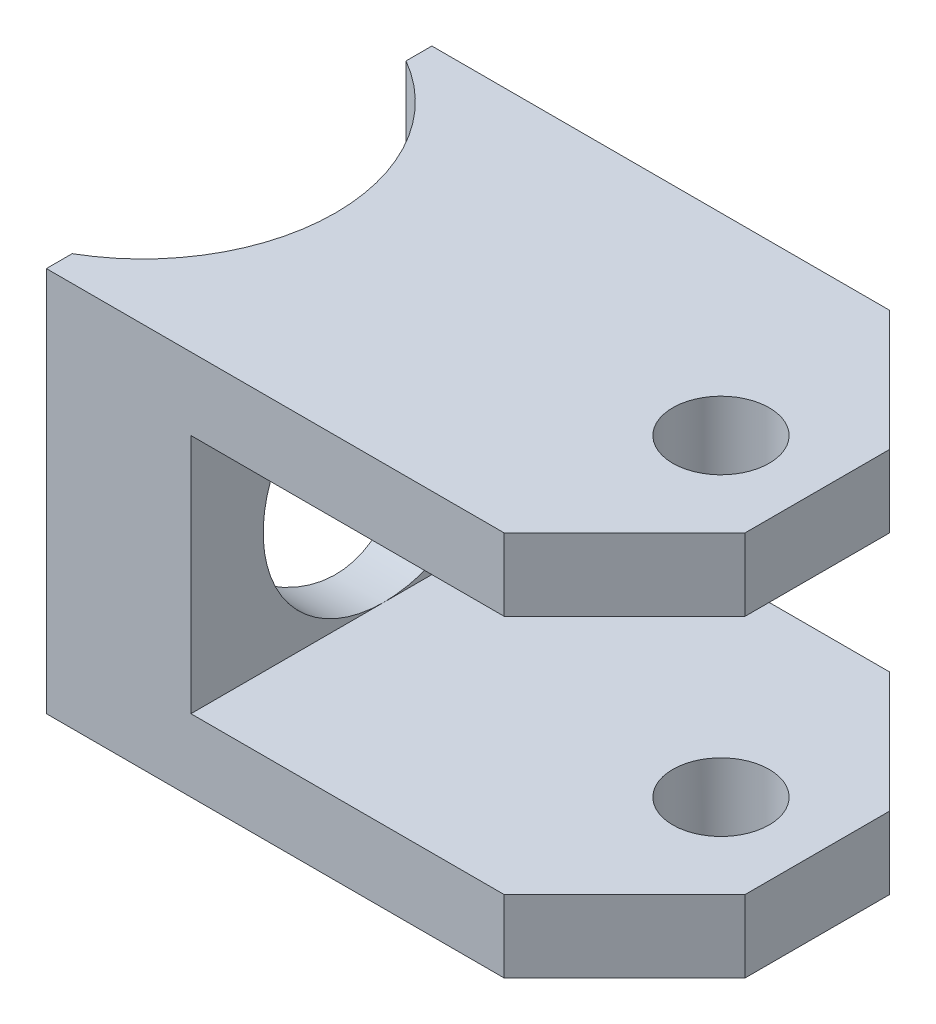
SolidWorks part; units mm, degrees
ref_plane "Front" through (0, 0, 0) normal (0, 0, 1) x (1, 0, 0)
ref_plane "Top" through (0, 0, 0) normal (0, 1, 0) x (1, 0, 0)
ref_plane "Right" through (0, 0, 0) normal (1, 0, 0) x (0, 0, -1)
sketch "Sketch1" plane through (0, 0, 0) normal (0, 0, 1) x (1, 0, 0)
  line L0 (6.35, 12.7) -> (44.45, 12.7)
  line L1 (44.45, 12.7) -> (44.45, 7.9375)
  line L2 (44.45, 7.9375) -> (15.875, 7.9375)
  line L3 (15.875, 7.9375) -> (15.875, -7.9375)
  line L4 (0, 0) -> (44.45, 0) construction
  line L5 (38.1, 12.7) -> (38.1, 0) construction
  line L6 (6.35, 12.7) -> (6.35, -12.7)
  line L7 (44.45, -7.9375) -> (15.875, -7.9375)
  line L8 (44.45, -12.7) -> (44.45, -7.9375)
  line L9 (6.35, -12.7) -> (44.45, -12.7)
  point P1 (12.8049, 0)
  point P5 (12.7, 0)
  point P12 (15.875, 0)
  point P14 (0, 0)
  dimension "D2" = 7.9375
  dimension "D3" = 38.1
  dimension "D4" = 3.175
  dimension "D5" = 6.35
  dimension "D6" = 6.35
  dimension "D1" = 25.4
  dimension "D7" = 12.7
extrude "Boss-Extrude1" add sketch "Sketch1" along normal mid plane 25.4
sketch3d "Mating Sketch"
  line L0 (38.1, 12.7, 0) -> (38.1, -12.7, 0) construction
  line L1 (38.1, 0, 0) -> (0, 0, 0) construction
  line L2 (38.1, 12.7, 0) -> (38.1, 0, 0) construction
  point P3 (38.1, 0, 0)
  point P4 (0, 0, 0)
  point P11 (0, 0, 0)
  point P13 (0, 0, 0)
  point P14 (0, 0, 0)
hole_wizard "1/4 (0.25) Diameter Hole1" positions "Sketch2" profile "Sketch4" hole size "1/4" standard "ANSI Inch" end condition through all
sketch "Sketch2" plane through (0, 12.7, 0) normal (0, 1, 0) x (1, 0, 0)
  point P0 (38.1, 0)
  point P8 (0, 0)
  point P9 (38.1, -5.2417)
  point P10 (0, 0)
  point P11 (0, 0)
sketch "Sketch4" plane through (38.1, 12.7, 0) normal (1, 0, 0) x (0, 0, 1)
  line L0 (0, 0) -> (0, 25.4)
  line L1 (0, 25.4) -> (3.175, 25.4)
  line L2 (3.175, 25.4) -> (3.175, 0)
  line L5 (3.175, 0) -> (0, 0)
  line L11 (0, -6.35) -> (0, 107.95) construction
  dimension "Thru Hole Dia." = 6.35
  dimension "Thru Hole Depth" = 25.4
chamfer "Chamfer1" distance 7.9375 angle 45 4 edges at (44.45, 10.3188, -12.7) (44.45, -10.3188, -12.7) (44.45, -10.3188, 12.7) (44.45, 10.3188, 12.7)
sketch "Sketch6" plane through (15.875, 0, 0) normal (1, 0, 0) x (0, 0, -1)
  line L0 (-12.7, 0) -> (12.7, 0) construction
  circle A0 centre (0, 0) radius 7.9375
  point P4 (0, 0)
  point P7 (0, 0)
  point P8 (0, 0)
  point P9 (0, 0)
  dimension "D1" = 15.875
extrude "Cut-Extrude1" cut sketch "Sketch6" against normal through all
sketch "Sketch7" plane through (0, 12.7, 0) normal (0, 1, 0) x (1, 0, 0)
  circle A0 centre (0, 0) radius 12.7
  point P0 (0, 0)
  point P2 (12.7, 0)
extrude "Cut-Extrude2" cut sketch "Sketch7" against normal through all
move or copy body "Body-Move/Copy1" [suppressed] bodies to move or copy 104
move or copy body "Body-Move/Copy2" [suppressed] bodies to move or copy 104
equation "\"D2@Sketch1\"=(.375)/2+.125"
